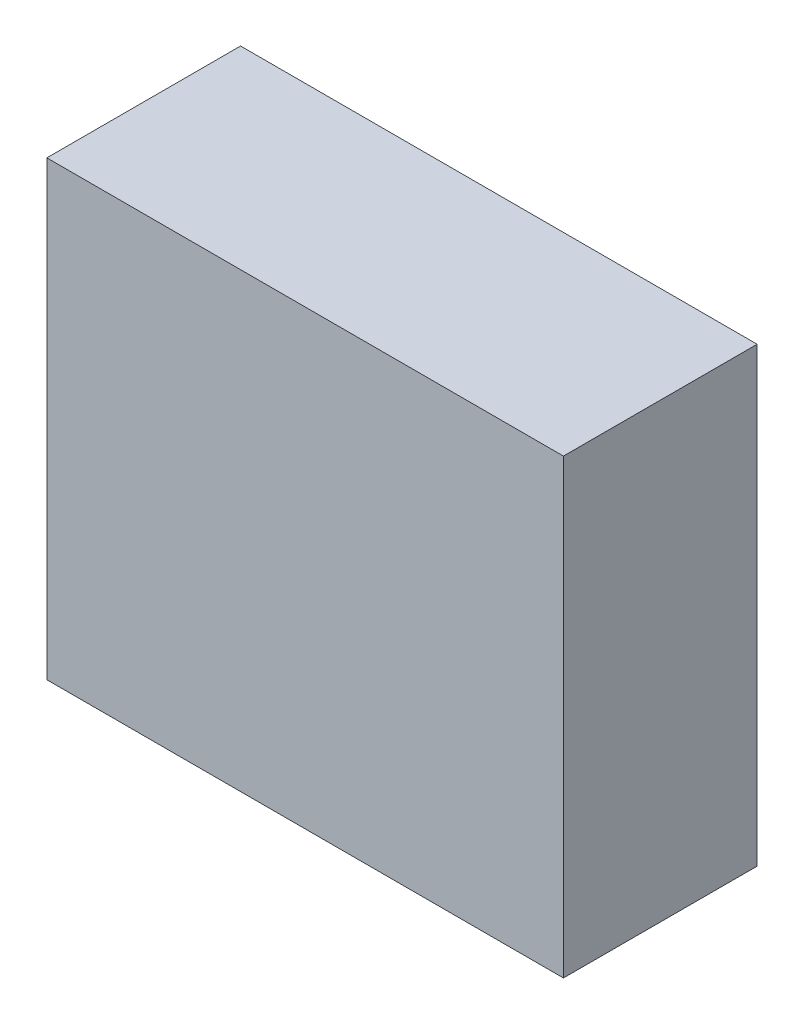
SolidWorks part; units mm, degrees
ref_plane "Front Plane" through (0, 0, 0) normal (0, 0, 1) x (1, 0, 0)
ref_plane "Top Plane" through (0, 0, 0) normal (0, 1, 0) x (1, 0, 0)
ref_plane "Right Plane" through (0, 0, 0) normal (1, 0, 0) x (0, 0, -1)
sketch "Sketch1" plane through (0, 0, 0) normal (0, 1, 0) x (1, 0, 0)
  line L1 (-203.2, -76.2) -> (203.2, -76.2)
  line L2 (-203.2, -76.2) -> (-203.2, 76.2)
  line L3 (-203.2, 76.2) -> (203.2, 76.2)
  line L4 (203.2, -76.2) -> (203.2, 76.2)
  line L5 (-203.2, -76.2) -> (203.2, 76.2) construction
  line L6 (-203.2, 76.2) -> (203.2, -76.2) construction
  point P0 (0, 0)
  dimension "D1" = 406.4
  dimension "D2" = 152.4
extrude "Boss-Extrude1" add sketch "Sketch1" along normal blind 355.6
